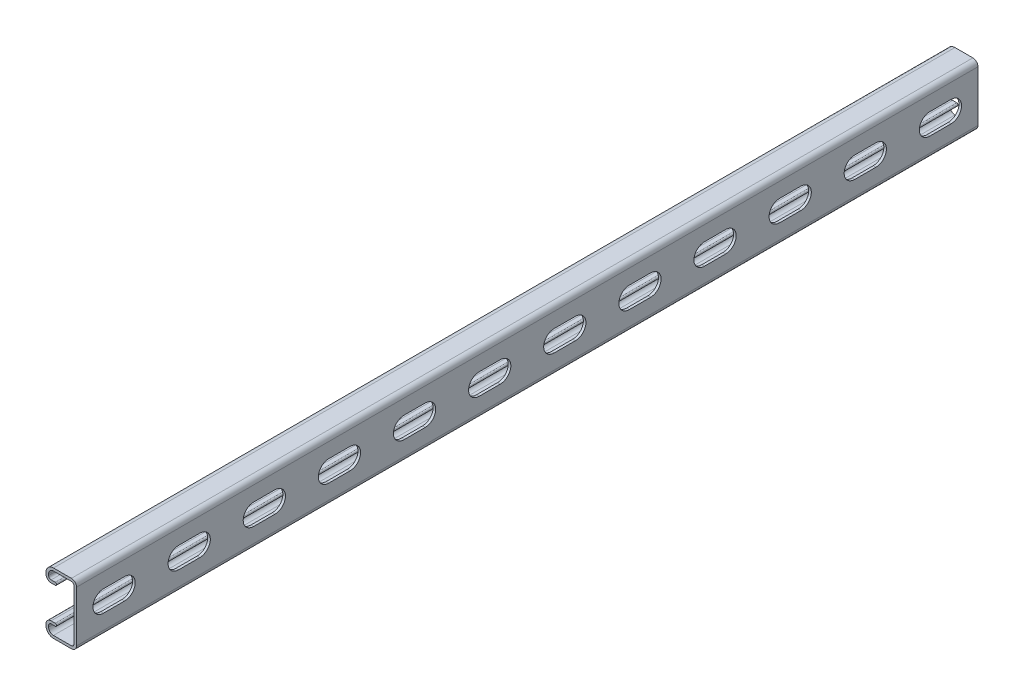
SolidWorks part; units mm, degrees
ref_plane "Front Plane" through (0, 0, 0) normal (0, 0, 1) x (1, 0, 0)
ref_plane "Top Plane" through (0, 0, 0) normal (0, 1, 0) x (1, 0, 0)
ref_plane "Right Plane" through (0, 0, 0) normal (1, 0, 0) x (0, 0, -1)
sketch "Sketch1" plane through (0, 0, 0) normal (0, 0, 1) x (1, 0, 0)
  line L0 (0, 0) -> (-20.6375, 0) construction
  line L3 (-20.6375, 20.6375) -> (0, 20.6375) construction
  line L4 (-20.6375, 20.6375) -> (-20.6375, -20.6375) construction
  line L5 (-20.6375, -20.6375) -> (0, -20.6375) construction
  line L6 (0, 20.6375) -> (0, -20.6375) construction
  line L7 (-15.5892, 20.6375) -> (-3.4607, 20.6375)
  line L8 (0, 17.1767) -> (0, -17.1767)
  line L9 (-1.778, -17.1767) -> (-1.778, 17.1767)
  line L10 (-3.4607, 18.8595) -> (-15.5892, 18.8595)
  line L11 (-20.6375, 15.5892) -> (-20.6375, 14.5732)
  line L12 (-17.1767, 11.1125) -> (-14.3891, 11.1125)
  line L14 (-14.3891, 12.8905) -> (-17.1767, 12.8905)
  line L15 (-18.8595, 14.5732) -> (-18.8595, 15.5892)
  line L16 (-18.8595, -14.5732) -> (-18.8595, -15.5892)
  line L17 (-14.3891, -12.8905) -> (-17.1767, -12.8905)
  line L18 (-17.1767, -11.1125) -> (-14.3891, -11.1125)
  line L19 (-20.6375, -15.5892) -> (-20.6375, -14.5732)
  line L20 (-3.4607, -18.8595) -> (-15.5892, -18.8595)
  line L21 (-15.5892, -20.6375) -> (-3.4607, -20.6375)
  line L22 (-1.778, -20.6375) -> (-1.778, 20.6375) construction
  arc A1 (0, 17.1767) -> (-3.4607, 20.6375) centre (-3.4607, 17.1767) ccw
  arc A2 (-1.778, 17.1767) -> (-3.4607, 18.8595) centre (-3.4607, 17.1767) ccw
  arc A4 (-15.5892, 20.6375) -> (-20.6375, 15.5892) centre (-15.5892, 15.5892) ccw
  arc A5 (-20.6375, 14.5732) -> (-17.1767, 11.1125) centre (-17.1767, 14.5732) ccw
  arc A6 (-14.3891, 11.1125) -> (-14.3891, 12.8905) centre (-14.3891, 12.0015) ccw
  arc A7 (-17.1767, 12.8905) -> (-18.8595, 14.5732) centre (-17.1767, 14.5732) cw
  arc A8 (-18.8595, 15.5892) -> (-15.5892, 18.8595) centre (-15.5892, 15.5892) cw
  arc A9 (-18.8595, -15.5892) -> (-15.5892, -18.8595) centre (-15.5892, -15.5892) ccw
  arc A10 (-17.1767, -12.8905) -> (-18.8595, -14.5732) centre (-17.1767, -14.5732) ccw
  arc A11 (-14.3891, -11.1125) -> (-14.3891, -12.8905) centre (-14.3891, -12.0015) cw
  arc A12 (-20.6375, -14.5732) -> (-17.1767, -11.1125) centre (-17.1767, -14.5732) cw
  arc A13 (-15.5892, -20.6375) -> (-20.6375, -15.5892) centre (-15.5892, -15.5892) cw
  arc A14 (-1.778, -17.1767) -> (-3.4607, -18.8595) centre (-3.4607, -17.1767) cw
  arc A15 (0, -17.1767) -> (-3.4607, -20.6375) centre (-3.4607, -17.1767) cw
  point P24 (0, 20.6375)
  point P65 (-1.778, 0)
  dimension "D1" = 3.4608
  dimension "D2" = 5.0482
  dimension "D3" = 3.4608
  dimension "Ht." = 20.6375
  dimension "Wd." = 41.275
  dimension "Thk." = 1.778
  dimension "D4" = 9.525
  dimension "D5" = 7.1374
extrude "Boss-Extrude1" add sketch "Sketch1" against normal blind 609.6
sketch "Sketch3" plane through (0, 0, 0) normal (1, 0, 0) x (0, 0, -1)
  line L0 (0, 0) -> (609.6, 0) construction
  point P2 (101.6, 0)
  point P3 (508, 0)
  dimension "D1" = 101.6
  dimension "D2" = 101.6
  dimension "D3" = 609.6
sketch "Sketch2" plane through (0, 0, 0) normal (1, 0, 0) x (0, 0, -1)
  line L0 (18.2562, 0) -> (32.5437, 0) construction
  line L1 (18.2562, 7.1437) -> (32.5437, 7.1437)
  line L2 (18.2562, -7.1437) -> (32.5437, -7.1437)
  line L3 (18.2562, 0) -> (0, 0) construction
  line L4 (25.4, 0) -> (76.2, 0) construction
  line L5 (0, -17.1767) -> (0, 17.1767) construction
  arc A0 (18.2562, 7.1437) -> (18.2562, -7.1437) centre (18.2562, 0) ccw
  arc A1 (32.5437, -7.1437) -> (32.5437, 7.1437) centre (32.5437, 0) ccw
  point P3 (25.4, 0)
  dimension "Slot Lg." = 28.575
  dimension "D2" = 25.4
  dimension "Slot Wd." = 14.2875
  dimension "Slot Ctr." = 50.8
  dimension "Hole to End" = 11.1125
extrude "Cut-Extrude1" cut sketch "Sketch2" against normal up to vertex (1.778 mm away) up to point (-1.778, 0, 0)
pattern_linear "LPattern1" count 12 spacing 50.8 along (0, 0, 1) of "Cut-Extrude1"
equation "\"D1@LPattern1\" = \"Slot Ctr.@Sketch2\""
equation "\"Hole Count@LPattern1\" = \"Lg.@Boss-Extrude1\" / \"D1@LPattern1\""
equation "\"D3@Sketch3\" = \"Lg.@Boss-Extrude1\""
